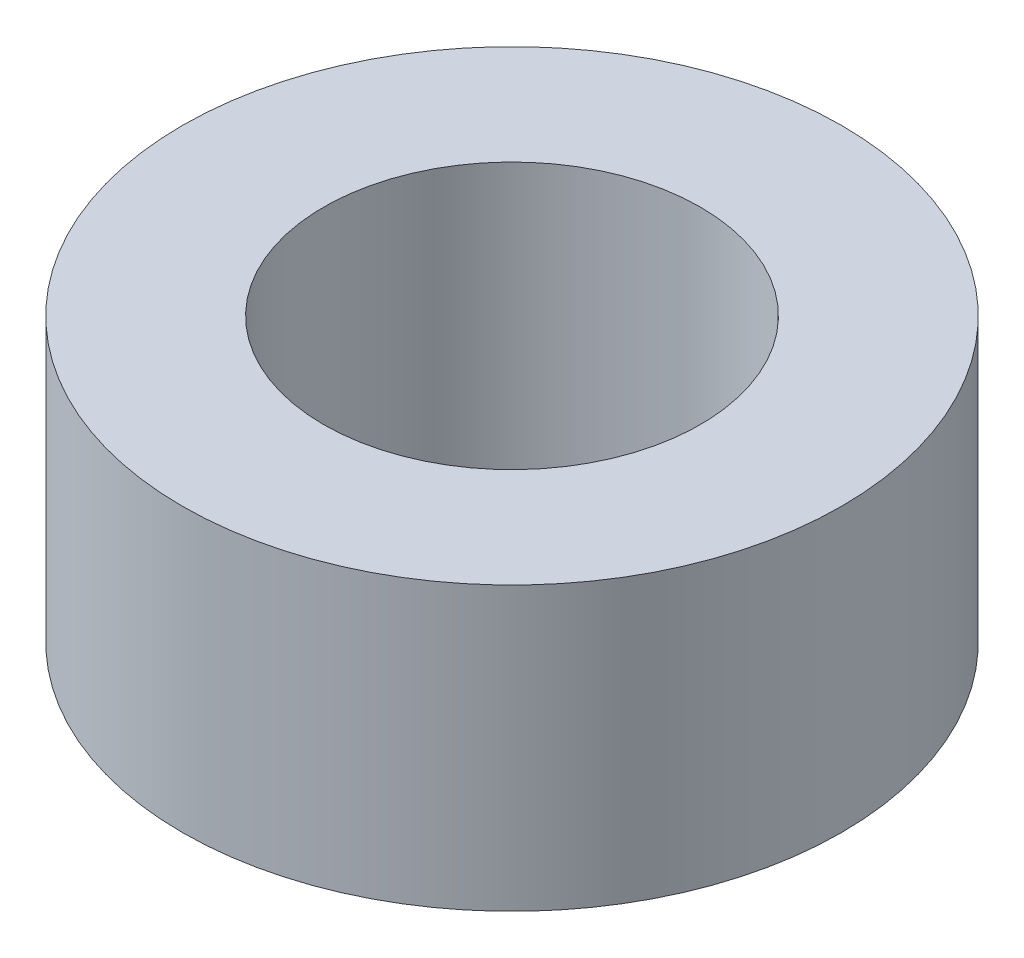
SolidWorks part; units mm, degrees
material "policarbonato"
ref_plane "Alzado" through (0, 0, 0) normal (0, 0, 1) x (1, 0, 0)
ref_plane "Planta" through (0, 0, 0) normal (0, 1, 0) x (1, 0, 0)
ref_plane "Vista lateral" through (0, 0, 0) normal (1, 0, 0) x (0, 0, -1)
sketch "Sketch1" plane through (0, 0, 0) normal (0, 1, 0) x (1, 0, 0)
  circle A0 centre (0, 0) radius 2
  circle A1 centre (0, 0) radius 3.5
  dimension "D1" = 4
  dimension "D2" = 7
extrude "Boss-Extrude1" add sketch "Sketch1" along normal blind 3
